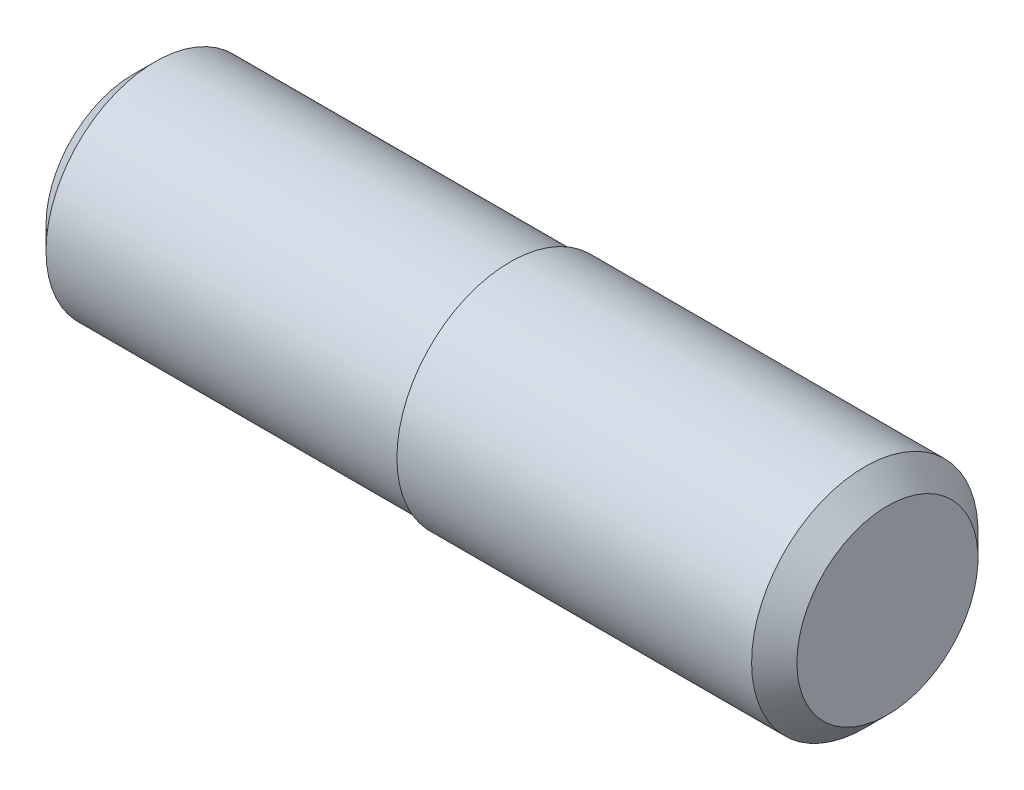
SolidWorks part; units mm, degrees
ref_plane "Front Plane" through (0, 0, 0) normal (0, 0, 1) x (1, 0, 0)
ref_plane "Top Plane" through (0, 0, 0) normal (0, 1, 0) x (1, 0, 0)
ref_plane "Right Plane" through (0, 0, 0) normal (1, 0, 0) x (0, 0, -1)
sketch "Sketch1" plane through (0, 0, 0) normal (0, 0, 1) x (1, 0, 0)
  line L0 (-2.5087, 0) -> (4.2137, 0) construction
  line L1 (-6.7925, 1.45) -> (-1.7925, 1.45)
  line L2 (-1.7925, 1.45) -> (-1.7925, 1.5)
  line L3 (-1.7925, 1.5) -> (3.2075, 1.5)
  line L4 (3.2075, 1.5) -> (3.2075, 0)
  line L5 (3.2075, 0) -> (-6.7925, 0)
  line L6 (-6.7925, 0) -> (-6.7925, 1.45)
  dimension "D1" = 1.45
  dimension "D2" = 1.5
  dimension "D3" = 5
  dimension "D4" = 5
revolve "Revolve1" add sketch "Sketch1" angle 360 about L0
chamfer "Chamfer1" distance 0.3 angle 45 2 edges at (3.2075, 0, 1.5) (-6.7925, 0, 1.45)
